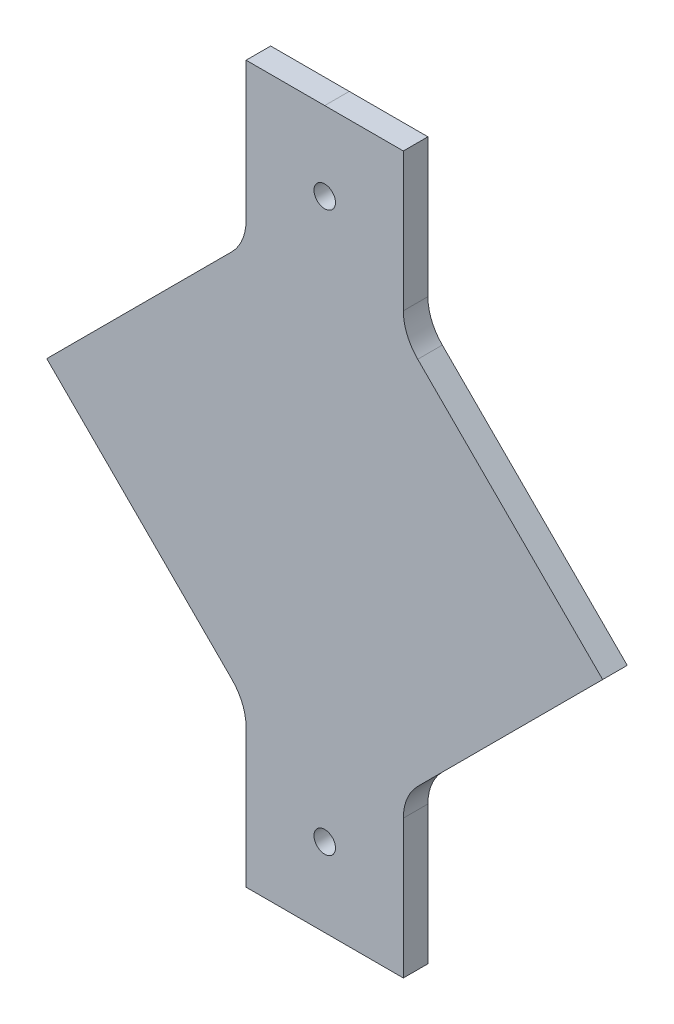
SolidWorks part; units mm, degrees
ref_plane "Front Plane" through (0, 0, 0) normal (0, 0, 1) x (1, 0, 0)
ref_plane "Top Plane" through (0, 0, 0) normal (0, 1, 0) x (1, 0, 0)
ref_plane "Right Plane" through (0, 0, 0) normal (1, 0, 0) x (0, 0, -1)
sketch "Sketch1" plane through (0, 0, 0) normal (0, 0, 1) x (1, 0, 0)
  line L0 (71.842, 0) -> (24.0397, 47.8023)
  line L1 (20.32, 92.5625) -> (-20.32, 92.5625)
  line L2 (20.32, 92.5625) -> (20.32, 56.7826)
  line L3 (21.2867, -51.9225) -> (-21.2867, -51.9225) construction
  line L4 (-20.32, 92.5625) -> (-20.32, 56.7826)
  line L5 (24.0397, 47.8023) -> (0, 71.842) construction
  line L6 (0, 71.842) -> (-24.0397, 47.8023) construction
  line L7 (20.32, -92.5625) -> (-20.32, -92.5625)
  line L8 (20.32, -92.5625) -> (20.32, -56.7826)
  line L10 (-20.32, -92.5625) -> (-20.32, -56.7826)
  line L12 (24.0397, -47.8023) -> (0, -71.842) construction
  line L13 (71.842, 0) -> (24.0397, -47.8023)
  line L14 (-24.0397, 47.8023) -> (-71.842, 0)
  line L15 (-24.0397, -47.8023) -> (-71.842, 0)
  line L16 (71.842, 0) -> (-71.842, 0) construction
  line L17 (0, 92.5625) -> (0, -92.162) construction
  line L18 (0, -71.842) -> (-24.0397, -47.8023) construction
  line L19 (21.2867, 51.9225) -> (-21.2867, 51.9225) construction
  circle A0 centre (0, 72.2425) radius 2.7781
  circle A1 centre (0, -72.2425) radius 2.7781
  arc A2 (24.0397, 47.8023) -> (20.32, 56.7826) centre (33.02, 56.7826) cw
  arc A3 (-20.32, 56.7826) -> (-24.0397, 47.8023) centre (-33.02, 56.7826) cw
  arc A4 (-24.0397, -47.8023) -> (-20.32, -56.7826) centre (-33.02, -56.7826) cw
  arc A5 (20.32, -56.7826) -> (24.0397, -47.8023) centre (33.02, -56.7826) cw
  point P0 (0, 71.842)
  point P5 (-0.8608, -68.9805)
  point P11 (0, 0)
  dimension "D7" = 5.5562
  dimension "D2" = 12.7
  dimension "D8" = 12.7
  dimension "D9" = 12.7
  dimension "D6" = 20.32
  dimension "D1" = 40.64
  dimension "D3" = 40.64
  dimension "D4" = 40.64
  dimension "D5" = 101.6
  dimension "D10" = 20.32
  dimension "D11" = 40.64
extrude "Extrude1" add sketch "Sketch1" along normal blind 6.35
ref_plane "Plane1" through (0, 101.6, 0) normal (0, 1, 0) x (-1, 0, 0)
ref_plane "Plane2" through (0, -101.6, 0) normal (0, 1, 0) x (-1, 0, 0)
sketch "Sketch4" plane through (0, 101.6, 0) normal (0, 1, 0) x (-1, 0, 0)
  line L0 (0, -16.52) -> (0, 19.2593)
sketch "Sketch5" plane through (0, -101.6, 0) normal (0, 1, 0) x (-1, 0, 0)
  line L0 (0, 23.14) -> (0, -37.6969)
split line "Split Line1"
split line "Split Line2"
